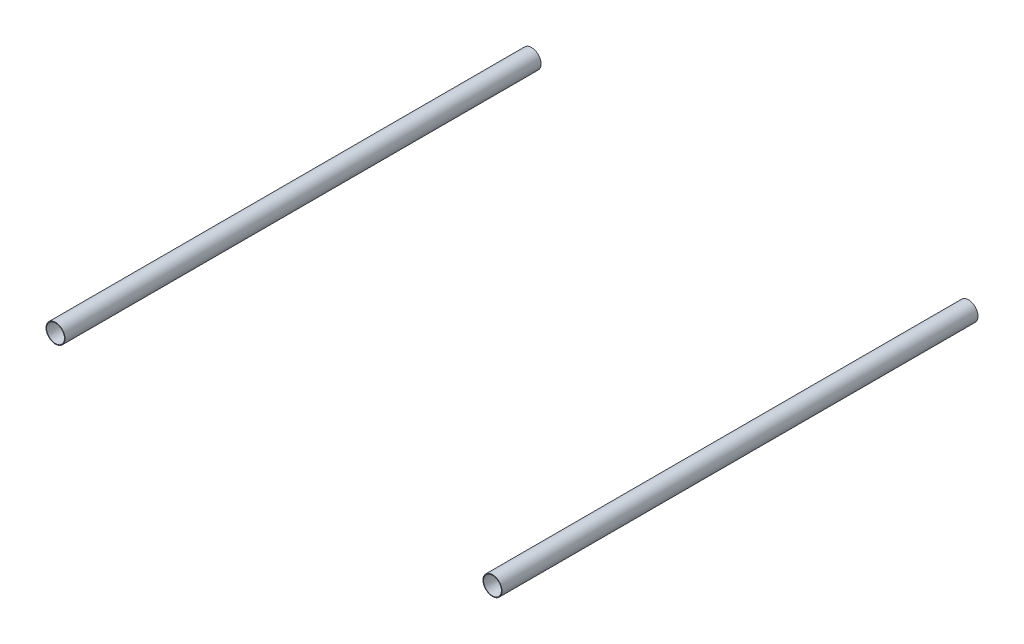
SolidWorks part; units mm, degrees
material "6063-T1"
ref_plane "Front" through (0, 0, 0) normal (0, 0, 1) x (1, 0, 0)
ref_plane "Top" through (0, 0, 0) normal (0, 1, 0) x (1, 0, 0)
ref_plane "Right" through (0, 0, 0) normal (1, 0, 0) x (0, 0, -1)
sketch "Sketch1" plane through (0, 0, 0) normal (0, 0, 1) x (1, 0, 0)
  line L0 (0, 0) -> (-2295, 0) construction
  circle A0 centre (0, 0) radius 50
  circle A1 centre (-2295, 0) radius 50
  dimension "D1" = 100
  dimension "D2" = 2295
extrude "Extrude-Thin1" add sketch "Sketch1" along normal blind 2500 thin thin type one direction reverse wall 3
